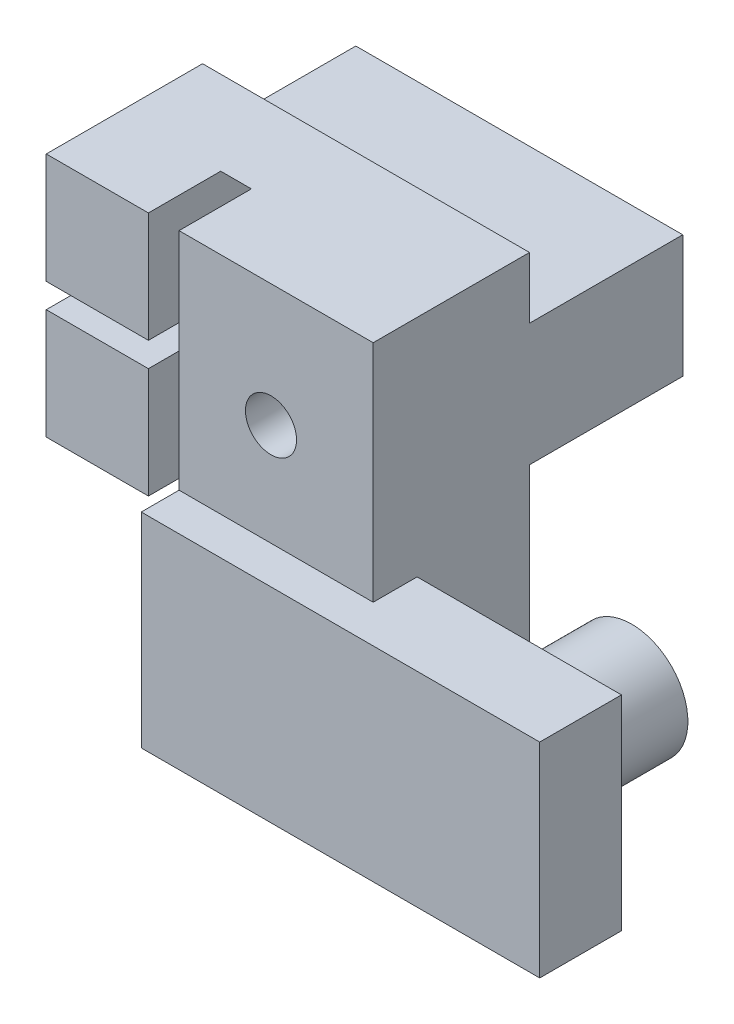
SolidWorks part; units mm, degrees
ref_plane "Спереди" through (0, 0, 0) normal (0, 0, 1) x (1, 0, 0)
ref_plane "Сверху" through (0, 0, 0) normal (0, 1, 0) x (1, 0, 0)
ref_plane "Справа" through (0, 0, 0) normal (1, 0, 0) x (0, 0, -1)
sketch "Эскиз1" plane through (0, 0, 0) normal (0, 0, 1) x (1, 0, 0)
  line L5 (-21.5997, 19) -> (-5.5997, 19)
  line L6 (-21.5997, 19) -> (-21.5997, 31)
  line L7 (-21.5997, 31) -> (-5.5997, 31)
  line L8 (-5.5997, 19) -> (-5.5997, 31)
  line L9 (-27.7383, 25) -> (-3.9171, 25) construction
  dimension "D1" = 12
  dimension "D2" = 16
extrude "Бобышка-Вытянуть1" add sketch "Эскиз1" along normal up to surface (7.65 mm away)
sketch "Эскиз2" plane through (0, 0, 7.65) normal (0, 0, 1) x (1, 0, 0)
  line L1 (-26.7383, 25) -> (-2.2483, 25) construction
  line L2 (-26.7383, 18) -> (-26.7383, 32) construction
  line L4 (-21.5997, 31) -> (-21.5997, 19) construction
  line L5 (-21.5997, 25.6) -> (-16.5997, 25.6)
  line L6 (-21.5997, 25.6) -> (-21.5997, 24.4)
  line L7 (-21.5997, 24.4) -> (-16.5997, 24.4)
  line L8 (-16.5997, 25.6) -> (-16.5997, 24.4)
  dimension "D1" = 1.2
  dimension "D2" = 5
extrude "Вырез-Вытянуть1" cut sketch "Эскиз2" against normal blind 4.5
sketch "Эскиз3" plane through (-16.5997, 0, 0) normal (-1, 0, 0) x (0, 0, 1)
  circle A0 centre (8, 25) radius 7.15
  dimension "D1" = 14.3
extrude "Вырез-Вытянуть2" cut sketch "Эскиз3" against normal blind 1.5
sketch "Эскиз4" plane through (0, 0, 0) normal (0, 0, -1) x (-1, 0, 0)
  line L0 (5.5997, 19) -> (5.5997, 31) construction
  line L1 (5.5997, 28) -> (21.5997, 28)
  line L2 (5.5997, 28) -> (5.5997, 22)
  line L3 (5.5997, 22) -> (21.5997, 22)
  line L4 (21.5997, 28) -> (21.5997, 22)
  line L5 (21.5997, 31) -> (21.5997, 19) construction
  line L6 (5.5997, 31) -> (21.5997, 31) construction
  dimension "D1" = 6
  dimension "D2" = 3
extrude "Бобышка-Вытянуть2" add sketch "Эскиз4" along normal blind 7.5
sketch "Эскиз5" plane through (0, 0, -7.5) normal (0, 0, -1) x (-1, 0, 0)
  line L0 (5.5997, 28) -> (5.5997, 22) construction
  line L2 (21.5997, 19) -> (5.5997, 19) construction
  circle A0 centre (10.5997, 25) radius 2.25
  dimension "D1" = 4.5
  dimension "D2" = 5
  dimension "D3" = 6
extrude "Вырез-Вытянуть3" cut sketch "Эскиз5" against normal up to surface (7.5 mm away) up to face at (-13.5997, 29.5, 0)
sketch "Эскиз6" plane through (0, 0, 0) normal (0, 0, -1) x (-1, 0, 0)
  circle A0 centre (10.5997, 25) radius 1.25
  dimension "D1" = 2.5
extrude "Вырез-Вытянуть4" cut sketch "Эскиз6" against normal through all
sketch "Эскиз7" plane through (0, 19, 0) normal (0, -1, 0) x (1, 0, 0)
  line L1 (-15.0997, 7.65) -> (-5.5997, 7.65)
  line L2 (-15.0997, 7.65) -> (-15.0997, 0)
  line L3 (-15.0997, 0) -> (-5.5997, 0)
  line L4 (-5.5997, 7.65) -> (-5.5997, 0)
extrude "Бобышка-Вытянуть3" add sketch "Эскиз7" along normal blind 9
sketch "Эскиз8" plane through (-5.5997, 0, 0) normal (1, 0, 0) x (0, 0, -1)
  line L0 (0, 10) -> (-7.65, 10) construction
  line L1 (-5.5, 10) -> (-9.5, 10)
  line L2 (-5.5, 10) -> (-5.5, 20)
  line L3 (-5.5, 20) -> (-9.5, 20)
  line L4 (-9.5, 10) -> (-9.5, 20)
  line L5 (0, 10) -> (0, 22) construction
  dimension "D1" = 10
  dimension "D2" = 4
  dimension "D3" = 5.5
extrude "Бобышка-Вытянуть4" add sketch "Эскиз8" along normal blind 10 and the other way up to vertex
sketch "Эскиз9" plane through (0, 0, 5.5) normal (0, 0, -1) x (-1, 0, 0)
  circle A0 centre (0.5997, 15) radius 2.75
  dimension "D1" = 5.5
extrude "Бобышка-Вытянуть5" add sketch "Эскиз9" along normal blind 5.5
